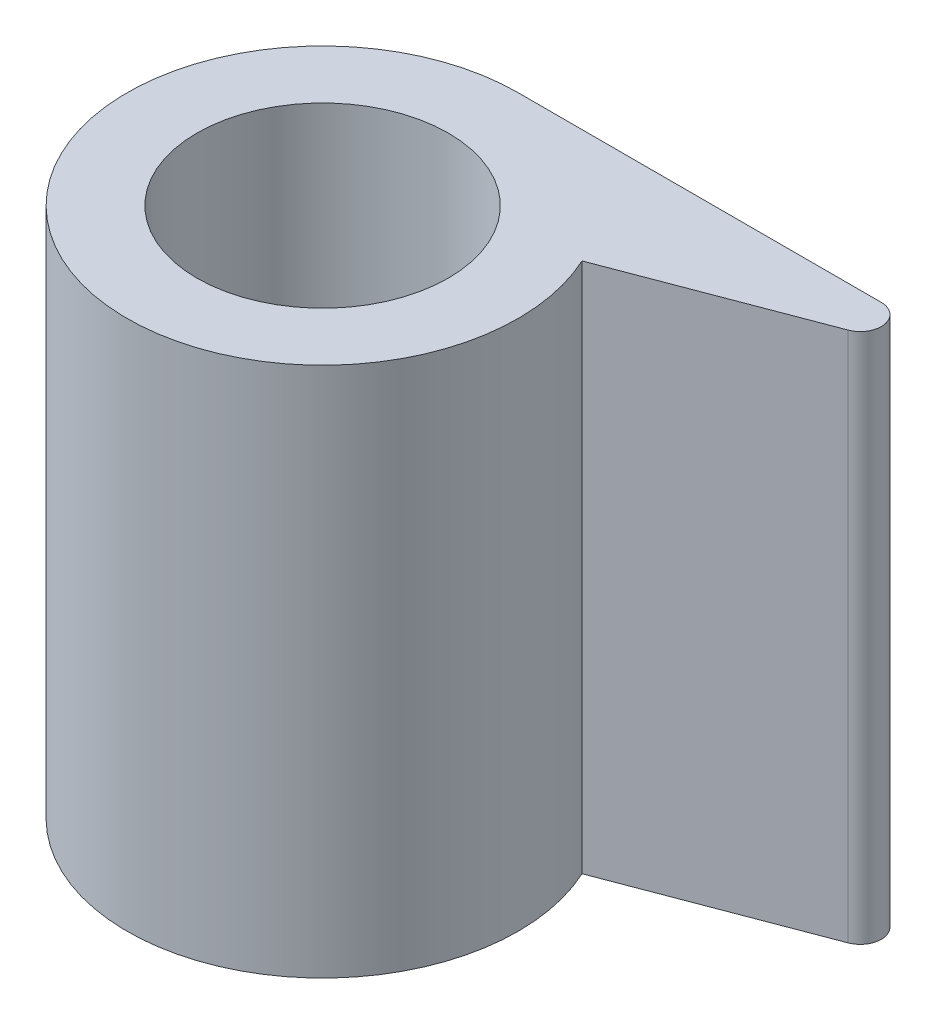
SolidWorks part; units mm, degrees
ref_plane "Alzado" through (0, 0, 0) normal (0, 0, 1) x (1, 0, 0)
ref_plane "Planta" through (0, 0, 0) normal (0, 1, 0) x (1, 0, 0)
ref_plane "Vista lateral" through (0, 0, 0) normal (1, 0, 0) x (0, 0, -1)
sketch "Croquis2" plane through (0, 0, 0) normal (0, 1, 0) x (1, 0, 0)
  line L0 (-13.873, 8.1169) -> (-0.873, 8.1169)
  line L1 (-0.6071, 6.6656) -> (-7.5152, 4.0456)
  arc A0 (-13.873, 8.1169) -> (-7.5152, 4.0456) centre (-13.873, 1.1169) ccw
  arc A1 (-0.873, 8.1169) -> (-0.6071, 6.6656) centre (-0.873, 7.3669) cw
  dimension "D1" = 14
  dimension "D3" = 0.75
  dimension "D2" = 13
extrude "Saliente-Extruir1" add sketch "Croquis2" along normal blind 19
sketch "Croquis3" plane through (0, 19, 0) normal (0, 1, 0) x (1, 0, 0)
  circle A0 centre (-13.873, 1.1169) radius 4.5
  dimension "D1" = 9
extrude "Cortar-Extruir1" cut sketch "Croquis3" against normal blind 19 contours A0
